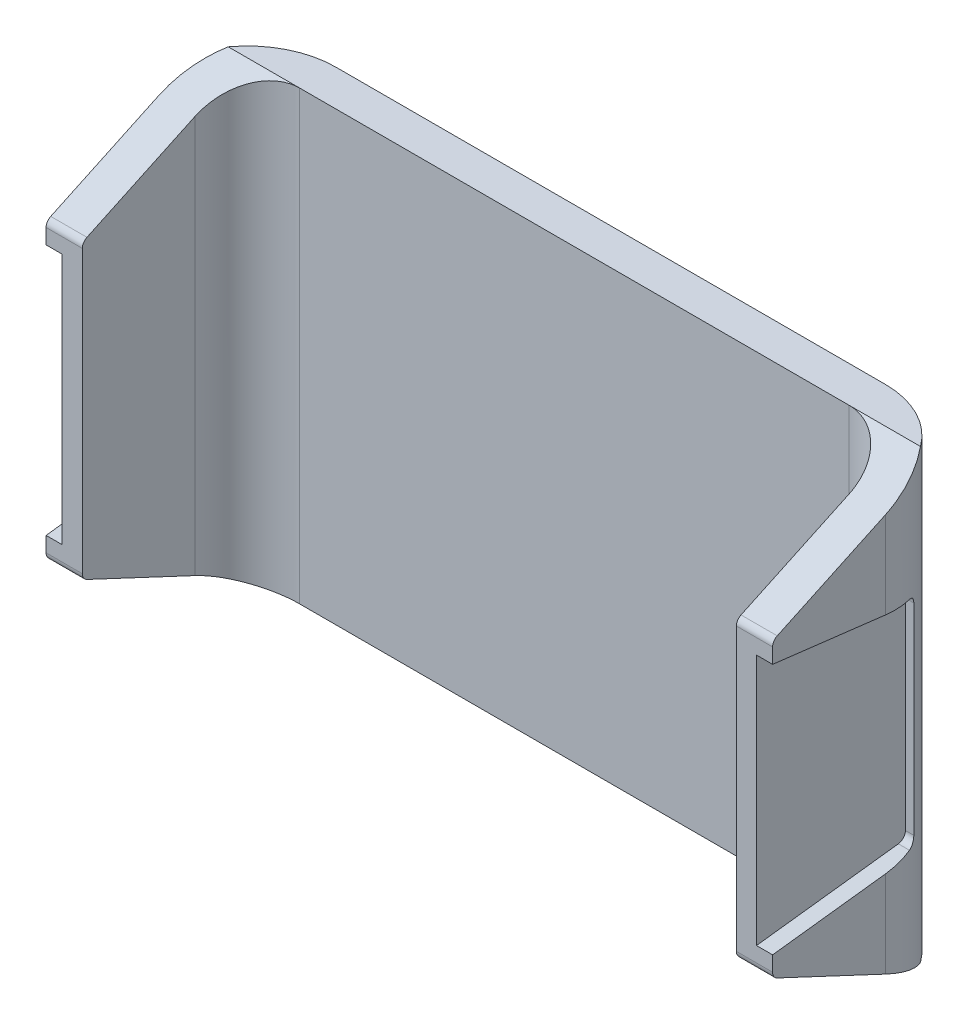
SolidWorks part; units mm, degrees
ref_plane "YZ" through (0, 0, 0) normal (0, 0, 1) x (1, 0, 0)
ref_plane "XY" through (0, 0, 0) normal (0, 1, 0) x (1, 0, 0)
ref_plane "XZ" through (0, 0, 0) normal (1, 0, 0) x (0, 0, -1)
sketch "Sketch1" plane through (0, 0, 0) normal (0, 1, 0) x (1, 0, 0)
  line L0 (20.6375, 0) -> (20.6375, 7.112)
  line L1 (17.3355, 10.414) -> (-17.3355, 10.414)
  line L2 (-20.6375, 7.112) -> (-20.6375, 0)
  line L3 (20.6375, 0) -> (-20.6375, 0) construction
  line L4 (0, 0) -> (0, 10.414) construction
  arc A0 (17.3355, 10.414) -> (20.6375, 7.112) centre (17.3355, 7.112) cw
  arc A1 (-17.3355, 10.414) -> (-20.6375, 7.112) centre (-17.3355, 7.112) ccw
  dimension "D2" = 3.302
  dimension "D3" = 10.414
  dimension "D1" = 41.275
extrude "Base-Extrude-Thin" add sketch "Sketch1" along normal mid plane 28.194 thin
sketch "Sketch2" plane through (22.9235, 0, 0) normal (1, 0, 0) x (0, 0, -1)
  line L0 (10.414, 14.097) -> (0.2923, 9.3499)
  line L1 (0, 14.097) -> (0, -14.097) construction
  line L2 (0, 8.89) -> (0, -8.89)
  line L3 (0.2923, -9.3499) -> (10.414, -14.097)
  arc A0 (0, 8.89) -> (0.2923, 9.3499) centre (0.508, 8.89) cw
  arc A1 (0.2923, -9.3499) -> (0, -8.89) centre (0.508, -8.89) cw
  dimension "D1" = 0.508
  dimension "D2" = 0.508
  dimension "D3" = 17.78
extrude "Cut-Extrude1" cut sketch "Sketch2" against normal through all flip side to cut
sketch "Sketch4" plane through (22.9235, 0, 0) normal (1, 0, 0) x (0, 0, -1)
  line L0 (0, 7.9375) -> (8.951, 6.8543)
  line L1 (0, 8.89) -> (0, -8.89) construction
  line L2 (9.398, 6.35) -> (9.398, -6.35)
  line L3 (8.951, -6.8543) -> (0, -7.9375)
  line L4 (0, 0) -> (9.398, 0) construction
  line L5 (0, 7.9375) -> (0, -7.9375)
  arc A0 (8.951, 6.8543) -> (9.398, 6.35) centre (8.89, 6.35) cw
  arc A1 (9.398, -6.35) -> (8.951, -6.8543) centre (8.89, -6.35) cw
  dimension "D1" = 0.508
  dimension "D2" = 0.508
  dimension "D3" = 9.398
  dimension "D4" = 15.875
  dimension "D5" = 12.7
extrude "Cut-Extrude2" cut sketch "Sketch4" against normal blind 1.016
sketch "Sketch5" plane through (-22.9235, 0, 0) normal (-1, 0, 0) x (0, 0, 1)
  line L4 (0, 7.9375) -> (0, -7.9375)
  line L5 (0, -7.9375) -> (-8.951, -6.8543)
  line L6 (-9.398, -6.35) -> (-9.398, 6.35)
  line L7 (-8.951, 6.8543) -> (0, 7.9375)
  line L8 (0, 7.9375) -> (0, -7.9375)
  line L9 (0, -7.9375) -> (-8.951, -6.8543)
  line L10 (-9.398, -6.35) -> (-9.398, 6.35)
  line L11 (-8.951, 6.8543) -> (0, 7.9375)
  arc A2 (-9.398, -6.35) -> (-8.951, -6.8543) centre (-8.89, -6.35) ccw
  arc A3 (-8.951, 6.8543) -> (-9.398, 6.35) centre (-8.89, 6.35) ccw
  arc A4 (-9.398, -6.35) -> (-8.951, -6.8543) centre (-8.89, -6.35) ccw
  arc A5 (-8.951, 6.8543) -> (-9.398, 6.35) centre (-8.89, 6.35) ccw
  dimension "D1" = 0
extrude "Cut-Extrude3" cut sketch "Sketch5" against normal blind 1.016
